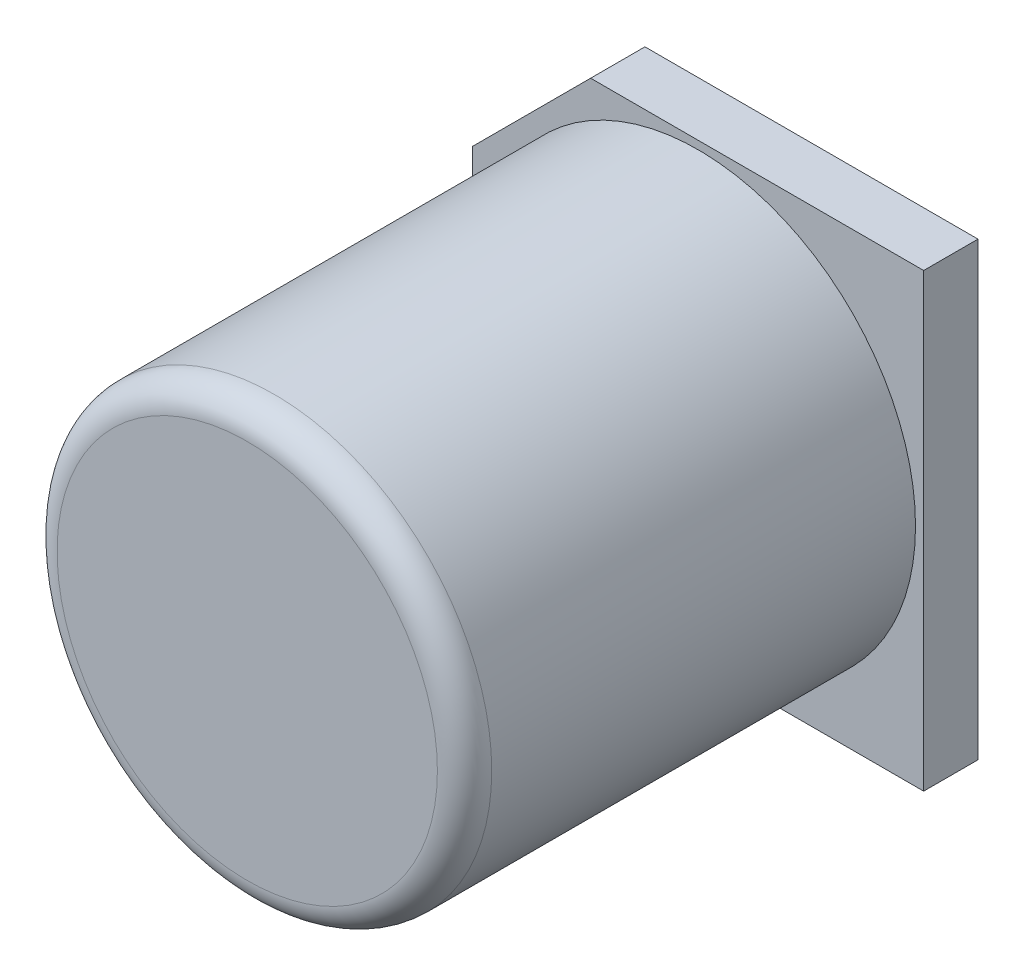
SolidWorks part; units mm, degrees
ref_plane "Front Plane" through (0, 0, 0) normal (0, 0, 1) x (1, 0, 0)
ref_plane "Top Plane" through (0, 0, 0) normal (0, 1, 0) x (1, 0, 0)
ref_plane "Right Plane" through (0, 0, 0) normal (1, 0, 0) x (0, 0, -1)
sketch "Sketch2" plane through (0, 0, 0) normal (0, 0, 1) x (1, 0, 0)
  line L0 (-1.98, 4.15) -> (-4.15, 1.98)
  line L1 (4.15, 4.15) -> (-1.98, 4.15)
  line L2 (4.15, 4.15) -> (4.15, -4.15)
  line L3 (4.15, -4.15) -> (-1.98, -4.15)
  line L4 (-4.15, 1.98) -> (-4.15, -1.98)
  line L5 (4.15, 4.15) -> (-4.15, -4.15) construction
  line L6 (4.15, -4.15) -> (-4.15, 4.15) construction
  line L7 (-1.98, -4.15) -> (-4.15, -1.98)
  point P0 (0, 0)
  dimension "D1" = 8.3
  dimension "D2" = 8.3
extrude "Boss-Extrude1" add sketch "Sketch2" along normal blind 1
sketch "Sketch3" plane through (0, 0, 1) normal (0, 0, 1) x (1, 0, 0)
  circle A0 centre (0, 0) radius 4
  dimension "D1" = 8
extrude "Boss-Extrude2" add sketch "Sketch3" along normal blind 8.3
fillet "Fillet2" radius 0.5 1 edges at (4, 0, 9.3)
